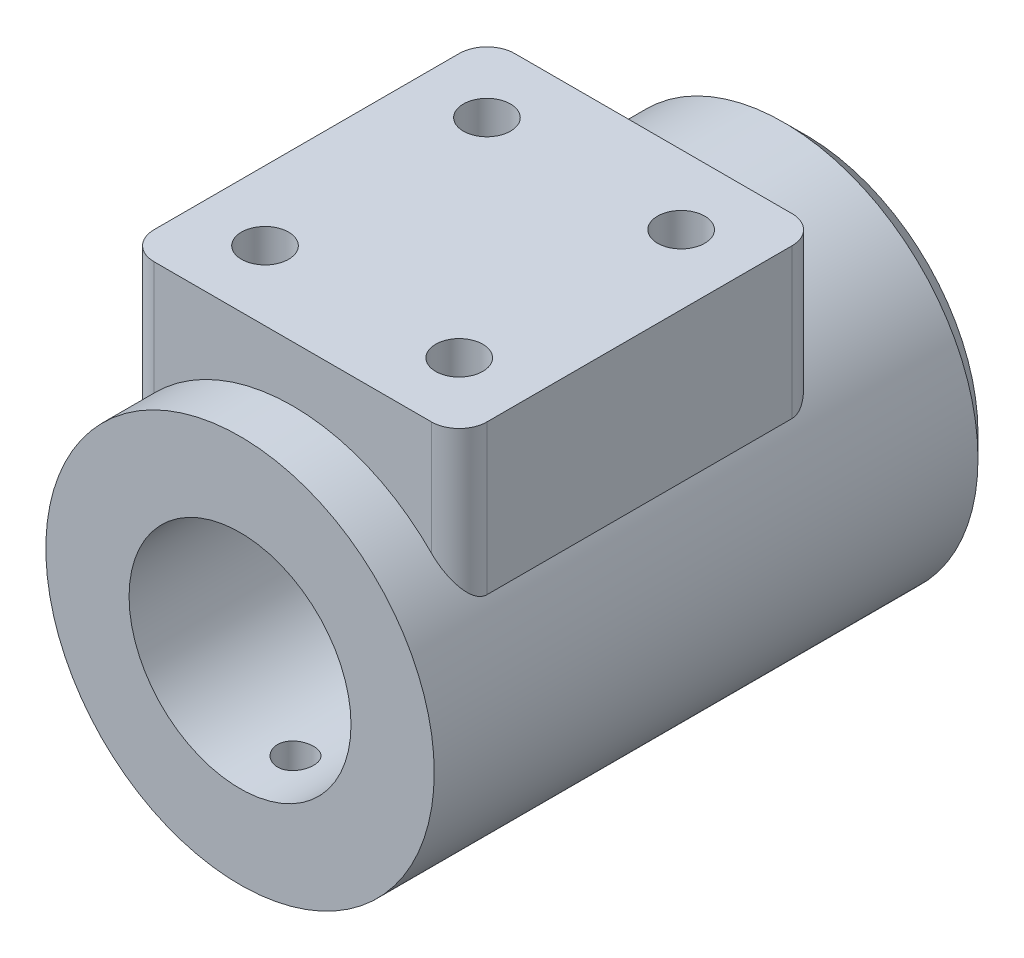
SolidWorks part; units mm, degrees
ref_plane "Plano frontal" through (0, 0, 0) normal (0, 0, 1) x (1, 0, 0)
ref_plane "Plano superior" through (0, 0, 0) normal (0, 1, 0) x (1, 0, 0)
ref_plane "Plano direito" through (0, 0, 0) normal (1, 0, 0) x (0, 0, -1)
sketch "Esboço1" plane through (0, 0, 0) normal (0, 0, 1) x (1, 0, 0)
  circle A0 centre (0, 0) radius 35
  dimension "D1" = 70
extrude "Ressalto-extrusão1" add sketch "Esboço1" along normal mid plane 102
sketch "Esboço3" plane through (0, 0, 0) normal (0, 1, 0) x (1, 0, 0)
  line L1 (-25, -41.5) -> (25, -41.5)
  line L2 (-30, -36.5) -> (-30, 18.5)
  line L3 (-25, 23.5) -> (25, 23.5)
  line L4 (30, -36.5) -> (30, 18.5)
  line L5 (-30, -41.5) -> (30, 23.5) construction
  line L6 (-30, 23.5) -> (30, -41.5) construction
  line L7 (-35, -51) -> (35, -51) construction
  arc A0 (-25, -41.5) -> (-30, -36.5) centre (-25, -36.5) cw
  arc A1 (30, -36.5) -> (25, -41.5) centre (25, -36.5) cw
  arc A2 (30, 18.5) -> (25, 23.5) centre (25, 18.5) ccw
  arc A3 (-25, 23.5) -> (-30, 18.5) centre (-25, 18.5) ccw
  point P0 (0, -9)
  dimension "D3" = 5
  dimension "D1" = 65
  dimension "D2" = 60
  dimension "D4" = 42
extrude "Ressalto-extrusão2" add sketch "Esboço3" along normal blind 45
sketch "Esboço2" plane through (0, 0, 0) normal (1, 0, 0) x (0, 0, -1)
  line L0 (-52.9579, 0) -> (56.196, 0) construction
  line L1 (51, 25) -> (42.2, 25)
  line L2 (51, -35) -> (51, 35) construction
  line L3 (16, 25) -> (16, 20)
  line L4 (16, 20) -> (-51, 20)
  line L5 (-51, 35) -> (-51, -35) construction
  line L6 (41, 25) -> (41, 26.5)
  line L7 (41, 26.5) -> (42.2, 26.5)
  line L8 (42.2, 26.5) -> (42.2, 25)
  line L10 (41, 25) -> (16, 25)
  line L11 (51, 25) -> (51, 0)
  line L12 (51, 0) -> (-51, 0)
  line L13 (-51, 0) -> (-51, 20)
  dimension "D1" = 35
  dimension "D2" = 25
  dimension "D3" = 20
  dimension "D4" = 25
  dimension "D5" = 1.2
  dimension "D6" = 26.5
revolve "Corte-Revolução1" cut sketch "Esboço2" angle 360 about L0
chamfer "Chanfro1" distance 4 angle 45 1 edges at (35, 0, -51)
sketch "Esboço4" plane through (0, 45, 0) normal (0, 1, 0) x (1, 0, 0)
  line L0 (-25, -41.5) -> (25, -41.5) construction
  circle A0 centre (-17.5, 11) radius 4.25
  circle A1 centre (17.5, 11) radius 4.25
  circle A2 centre (17.5, -29) radius 4.25
  circle A3 centre (-17.5, -29) radius 4.25
  dimension "D1" = 8.5
  dimension "D2" = 17.5
  dimension "D3" = 12.5
  dimension "D4" = 40
  dimension "D5" = 35
extrude "Corte-extrusão1" cut sketch "Esboço4" against normal blind 20
cosmetic thread "Representação de rosca1" parameters "D2"=10
cosmetic thread "Representação de rosca2" parameters "D2"=10
cosmetic thread "Representação de rosca3" parameters "D2"=10
cosmetic thread "Representação de rosca4" parameters "D2"=10
sketch "Esboço5" plane through (0, 0, 0) normal (0, 1, 0) x (1, 0, 0)
  line L0 (-35, -51) -> (35, -51) construction
  circle A0 centre (0, -41) radius 3.25
  dimension "D1" = 6.5
  dimension "D2" = 10
extrude "Corte-extrusão2" cut sketch "Esboço5" against normal through all
cosmetic thread "Representação de rosca5" parameters "D2"=8
